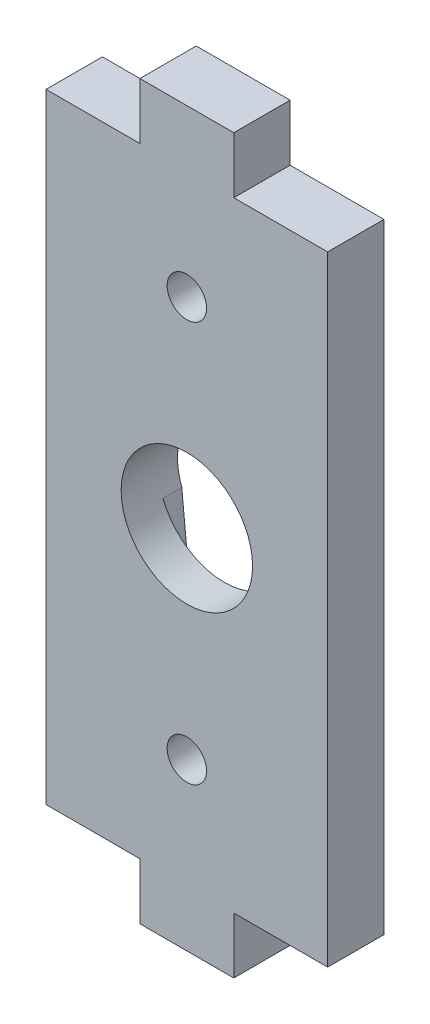
SolidWorks part; units mm, degrees
ref_plane "Alzado" through (0, 0, 0) normal (0, 0, 1) x (1, 0, 0)
ref_plane "Planta" through (0, 0, 0) normal (0, 1, 0) x (1, 0, 0)
ref_plane "Vista lateral" through (0, 0, 0) normal (1, 0, 0) x (0, 0, -1)
sketch "Corte exterior" plane through (0, 0, 0) normal (0, 0, 1) x (1, 0, 0)
  line L0 (49.5, 10.5) -> (54.5, 10.5)
  line L1 (54.5, 10.5) -> (54.5, 13.5)
  line L2 (54.5, 13.5) -> (59.5, 13.5)
  line L3 (59.5, 13.5) -> (59.5, 29.5)
  line L4 (59.5, 29.5) -> (59.5, 46.5)
  line L5 (59.5, 46.5) -> (54.5, 46.5)
  line L6 (54.5, 46.5) -> (54.5, 49.5)
  line L7 (54.5, 49.5) -> (49.5, 49.5)
  line L8 (49.5, 49.5) -> (49.5, 46.5)
  line L9 (49.5, 46.5) -> (44.5, 46.5)
  line L10 (44.5, 46.5) -> (44.5, 23.5)
  line L11 (44.5, 23.5) -> (44.5, 13.5)
  line L12 (44.5, 13.5) -> (49.5, 13.5)
  line L13 (49.5, 13.5) -> (49.5, 10.5)
  circle A0 centre (52, 40.6722) radius 1.05
  circle A1 centre (52, 19.3278) radius 1.05
  circle A2 centre (52, 30) radius 3.5
sketch "Grabado Superficie" plane through (0, 0, 0) normal (0, 0, 1) x (1, 0, 0)
  line L0 (48.7308, 28.75) -> (50, 15.7)
  line L1 (54, 15.7) -> (55.2692, 28.75)
  line L2 (55.2692, 31.25) -> (53.9903, 44.1966)
  line L3 (50, 44) -> (48.7308, 31.25)
  arc A0 (48.7308, 28.75) -> (55.2692, 28.75) centre (52, 30) ccw
  arc A1 (50, 15.7) -> (54, 15.7) centre (52, 15.7) ccw
  arc A2 (55.2692, 31.25) -> (48.7308, 31.25) centre (52, 30) ccw
  arc A3 (53.9903, 44.1966) -> (50, 44) centre (52, 44) ccw
extrude "Saliente-Extruir1" add sketch "Corte exterior" along normal blind 3
extrude "Cortar-Extruir1" cut sketch "Grabado Superficie" along normal blind 1
